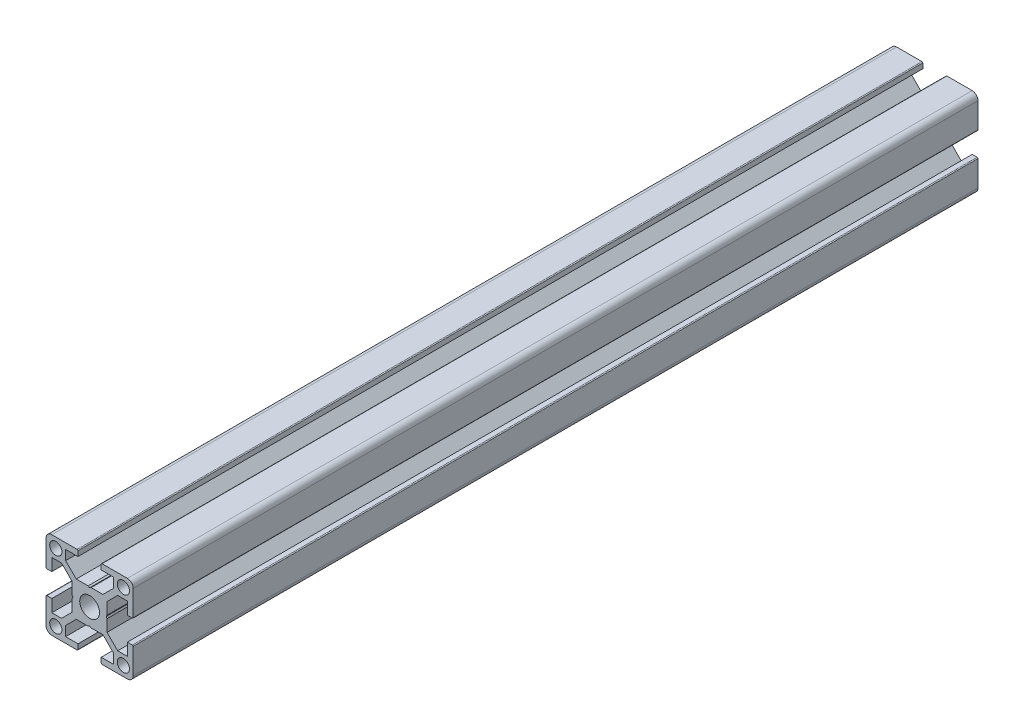
SolidWorks part; units mm, degrees
material "1060 合金"
ref_plane "前视基准面" through (0, 0, 0) normal (0, 0, 1) x (1, 0, 0)
ref_plane "上视基准面" through (0, 0, 0) normal (0, 1, 0) x (1, 0, 0)
ref_plane "右视基准面" through (0, 0, 0) normal (1, 0, 0) x (0, 0, -1)
sketch "草图1" plane through (0, 0, 0) normal (0, 0, 1) x (1, 0, 0)
  line B0 (5, 23.6667) -> (5, 17.8667)
  line B1 (5.2, 17.6667) -> (6.3333, 17.6667)
  line B2 (6.3333, 17.6667) -> (6.3333, 20.5)
  line B3 (6.3333, 20.5) -> (8.5572, 20.5)
  line B4 (8.5572, 20.5) -> (11, 18.0572)
  line B5 (11, 18.0572) -> (11, 15.3464)
  line B6 (11, 15.3464) -> (11.2, 15)
  line B7 (11.2, 15) -> (11, 14.6536)
  line B8 (11, 14.6536) -> (11, 11.9428)
  line B9 (11, 11.9428) -> (8.5572, 9.5)
  line B10 (8.5572, 9.5) -> (6.3333, 9.5)
  line B11 (6.3333, 9.5) -> (6.3333, 12.3333)
  line B12 (6.3333, 12.3333) -> (5.2, 12.3333)
  line B13 (5, 12.1333) -> (5, 6.3333)
  line B14 (6.3333, 5) -> (12.1333, 5)
  line B15 (12.3333, 5.2) -> (12.3333, 6.3333)
  line B16 (12.3333, 6.3333) -> (9.5, 6.3333)
  line B17 (9.5, 6.3333) -> (9.5, 8.5572)
  line B18 (9.5, 8.5572) -> (11.9428, 11)
  line B19 (11.9428, 11) -> (14.6536, 11)
  line B20 (14.6536, 11) -> (15, 11.2)
  line B21 (15, 11.2) -> (15.3464, 11)
  line B22 (15.3464, 11) -> (18.0572, 11)
  line B23 (18.0572, 11) -> (20.5, 8.5572)
  line B24 (20.5, 8.5572) -> (20.5, 6.3333)
  line B25 (20.5, 6.3333) -> (17.6667, 6.3333)
  line B26 (17.6667, 6.3333) -> (17.6667, 5.2)
  line B27 (17.8667, 5) -> (23.6667, 5)
  line B28 (25, 6.3333) -> (25, 12.1333)
  line B29 (24.8, 12.3333) -> (23.6667, 12.3333)
  line B30 (23.6667, 12.3333) -> (23.6667, 9.5)
  line B31 (23.6667, 9.5) -> (21.4428, 9.5)
  line B32 (21.4428, 9.5) -> (19, 11.9428)
  line B33 (19, 11.9428) -> (19, 14.6536)
  line B34 (19, 14.6536) -> (18.8, 15)
  line B35 (18.8, 15) -> (19, 15.3464)
  line B36 (19, 15.3464) -> (19, 18.0572)
  line B37 (19, 18.0572) -> (21.4428, 20.5)
  line B38 (21.4428, 20.5) -> (23.6667, 20.5)
  line B39 (23.6667, 20.5) -> (23.6667, 17.6667)
  line B40 (23.6667, 17.6667) -> (24.8, 17.6667)
  line B41 (25, 17.8667) -> (25, 23.6667)
  line B42 (23.6667, 25) -> (17.8667, 25)
  line B43 (17.6667, 24.8) -> (17.6667, 23.6667)
  line B44 (17.6667, 23.6667) -> (20.5, 23.6667)
  line B45 (20.5, 23.6667) -> (20.5, 21.4428)
  line B46 (20.5, 21.4428) -> (18.0572, 19)
  line B47 (18.0572, 19) -> (15.3464, 19)
  line B48 (15.3464, 19) -> (15, 18.8)
  line B49 (15, 18.8) -> (14.6536, 19)
  line B50 (14.6536, 19) -> (11.9428, 19)
  line B51 (11.9428, 19) -> (9.5, 21.4428)
  line B52 (9.5, 21.4428) -> (9.5, 23.6667)
  line B53 (9.5, 23.6667) -> (12.3333, 23.6667)
  line B54 (12.3333, 23.6667) -> (12.3333, 24.8)
  line B55 (12.1333, 25) -> (6.3333, 25)
  circle B56 centre (7.25, 22.75) radius 1.4
  circle B57 centre (22.75, 22.75) radius 1.4
  circle B58 centre (15, 15) radius 2.2667
  circle B59 centre (7.25, 7.25) radius 1.4
  circle B60 centre (22.75, 7.25) radius 1.4
  arc B61 (6.3333, 25) -> (5, 23.6667) centre (6.3333, 23.6667) ccw
  arc B62 (5, 17.8667) -> (5.2, 17.6667) centre (5.2, 17.8667) ccw
  arc B63 (5.2, 12.3333) -> (5, 12.1333) centre (5.2, 12.1333) ccw
  arc B64 (5, 6.3333) -> (6.3333, 5) centre (6.3333, 6.3333) ccw
  arc B65 (12.1333, 5) -> (12.3333, 5.2) centre (12.1333, 5.2) ccw
  arc B66 (17.6667, 5.2) -> (17.8667, 5) centre (17.8667, 5.2) ccw
  arc B67 (23.6667, 5) -> (25, 6.3333) centre (23.6667, 6.3333) ccw
  arc B68 (25, 12.1333) -> (24.8, 12.3333) centre (24.8, 12.1333) ccw
  arc B69 (24.8, 17.6667) -> (25, 17.8667) centre (24.8, 17.8667) ccw
  arc B70 (25, 23.6667) -> (23.6667, 25) centre (23.6667, 23.6667) ccw
  arc B71 (17.8667, 25) -> (17.6667, 24.8) centre (17.8667, 24.8) ccw
  arc B72 (12.3333, 24.8) -> (12.1333, 25) centre (12.1333, 24.8) ccw
sketch_block_instance "30X30-1"
sketch_block "30X30"
extrude "凸台-拉伸1" add sketch "草图1" along normal blind 193.8
